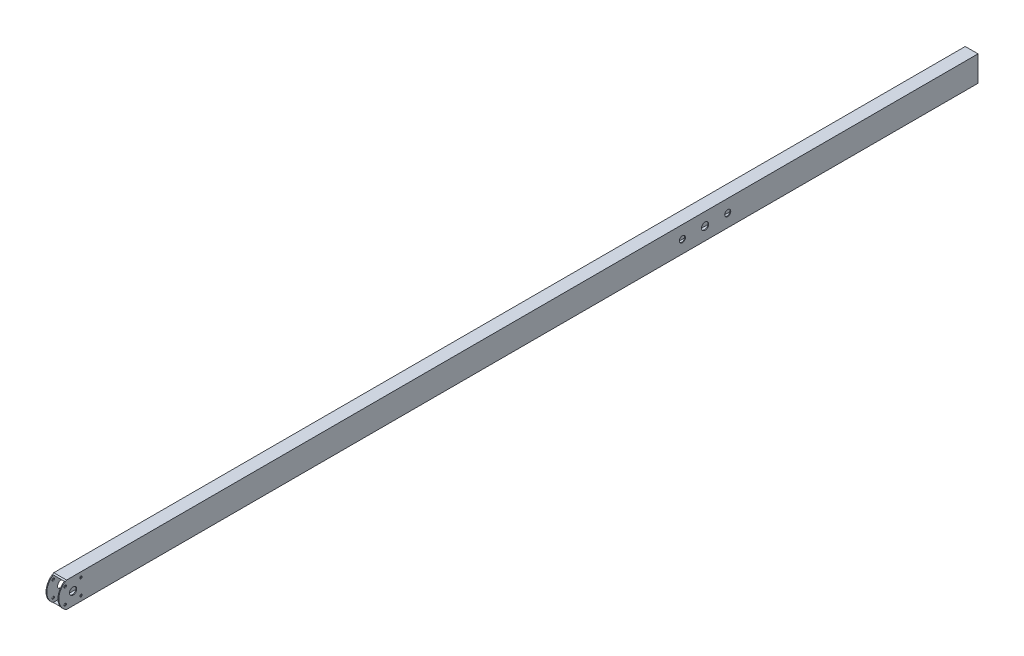
SolidWorks part; units mm, degrees
ref_plane "Front Plane" through (0, 0, 0) normal (0, 0, 1) x (1, 0, 0)
ref_plane "Top Plane" through (0, 0, 0) normal (0, 1, 0) x (1, 0, 0)
ref_plane "Right Plane" through (0, 0, 0) normal (1, 0, 0) x (0, 0, -1)
sketch "Sketch2" plane through (0, 0, 0) normal (0, 0, 1) x (1, 0, 0)
  line L1 (12.7, -25.4) -> (-12.7, -25.4)
  line L2 (12.7, -25.4) -> (12.7, 25.4)
  line L3 (12.7, 25.4) -> (-12.7, 25.4)
  line L4 (-12.7, -25.4) -> (-12.7, 25.4)
  line L5 (12.7, -25.4) -> (-12.7, 25.4) construction
  line L6 (12.7, 25.4) -> (-12.7, -25.4) construction
  point P1 (0, 0)
  dimension "D1" = 25.4
  dimension "D2" = 50.8
extrude "Extrude-Thin2" add sketch "Sketch2" along normal blind 1828.8 thin
sketch "Sketch8" plane through (12.7, 0, 0) normal (1, 0, 0) x (0, 0, -1)
  line L3 (-1800.225, -28.575) -> (-1800.225, 28.575)
  line L7 (0, -25.4) -> (0, 25.4)
  line L8 (0, 25.4) -> (-1828.8, 25.4)
  line L9 (-1828.8, 25.4) -> (-1828.8, -25.4)
  line L10 (-1828.8, -25.4) -> (0, -25.4)
  line L11 (0, -25.4) -> (0, 25.4)
  line L12 (0, 25.4) -> (-1828.8, 25.4)
  line L13 (-1828.8, 25.4) -> (-1828.8, -25.4)
  line L14 (-1828.8, -25.4) -> (0, -25.4)
  arc A0 (-1800.225, 28.575) -> (-1800.225, -28.575) centre (-1800.225, 0) ccw
  point P4 (-1828.8, 0)
  point P5 (-1828.8, 0)
  line M13 (-1828.8, 25.4) -> (-1828.8, -25.4)
  line M14 (-1828.8, -25.4) -> (0, -25.4)
  dimension "D2" = 57.15
  dimension "D1" = 0
extrude "Cut-Extrude1" cut sketch "Sketch8" against normal through all contours A0 L12 M13 | A0 L13 M14
hole_wizard "9/16 (0.5625) Diameter Hole1" positions "Sketch9" profile "Sketch10" hole size "9/16" standard "ANSI Inch" end condition through all
sketch "Sketch9" plane through (12.7, 0, 0) normal (1, 0, 0) x (0, 0, -1)
  arc A0 (-1813.3159, 25.4) -> (-1813.3159, -25.4) centre (-1800.225, 0) ccw construction
  point P0 (-1800.225, 0)
  point P3 (-1800.225, 0)
  point P4 (0, 0)
  point P5 (-1798.1492, 0)
  point P6 (0, 0)
  point P10 (-1828.8, 0)
  point P11 (0, 0)
  point P12 (-1800.225, 0)
sketch "Sketch10" plane through (12.7, 0, 1800.225) normal (0, 1, 0) x (0, 0, -1)
  line L0 (0, 0) -> (0, 25.4)
  line L1 (0, 25.4) -> (7.1437, 25.4)
  line L2 (7.1437, 25.4) -> (7.1437, 0)
  line L5 (7.1437, 0) -> (0, 0)
  line L11 (0, -6.35) -> (0, 107.95) construction
  dimension "Thru Hole Dia." = 14.2875
  dimension "Thru Hole Depth" = 25.4
sketch "Sketch3" plane through (12.7, 0, 0) normal (1, 0, 0) x (0, 0, -1)
  line L0 (-587.9703, 0) -> (-497.8797, 0)
  line L8 (-1813.3159, 25.4) -> (0, 25.4) construction
  line L9 (-1813.3159, -25.4) -> (0, -25.4) construction
  line L10 (-542.925, 25.4) -> (-542.925, -25.4) construction
  circle A0 centre (-1800.225, 0) radius 7.1438 construction
  point P0 (-542.925, 0)
  point P8 (-542.925, 0)
  point P18 (-542.925, 0)
  point P20 (-1796.2131, -1.0052)
  point P23 (-1763.649, 35.2561)
  dimension "D2" = 90.0906
  dimension "D1" = 1257.3
hole_wizard "9/16 (0.5625) Diameter Hole2" positions "Sketch4" profile "Sketch5" hole size "9/16" standard "ANSI Inch" end condition through all
sketch "Sketch4" plane through (12.7, 0, 0) normal (1, 0, 0) x (0, 0, -1)
  point P0 (-542.925, 0)
sketch "Sketch5" plane through (12.7, 0, 542.925) normal (0, 1, 0) x (0, 0, -1)
  line L0 (0, 0) -> (0, 25.4)
  line L1 (0, 25.4) -> (7.1437, 25.4)
  line L2 (7.1437, 25.4) -> (7.1437, 0)
  line L5 (7.1437, 0) -> (0, 0)
  line L11 (0, -6.35) -> (0, 107.95) construction
  dimension "Thru Hole Dia." = 14.2875
  dimension "Thru Hole Depth" = 25.4
hole_wizard "Ø12.0mm Dowel Hole1" positions "Sketch11" profile "Sketch12" hole size "Ø12.0" standard "ANSI Metric" end condition through all
sketch "Sketch11" plane through (12.7, 0, 0) normal (1, 0, 0) x (0, 0, -1)
  point P0 (-587.9703, 0)
  point P3 (-497.8797, 0)
sketch "Sketch12" plane through (12.7, 0, 587.9703) normal (0, 1, 0) x (0, 0, -1)
  line L0 (0, 0) -> (0, 25.4)
  line L1 (0, 25.4) -> (6, 25.4)
  line L2 (6, 25.4) -> (6, 0)
  line L5 (6, 0) -> (0, 0)
  line L11 (0, -6.35) -> (0, 107.95) construction
  dimension "Thru Hole Dia." = 12
  dimension "Thru Hole Depth" = 25.4
sketch "Sketch13" plane through (12.7, 0, 0) normal (1, 0, 0) x (0, 0, -1)
  circle A0 centre (-1800.225, 0) radius 27.813 construction
  circle A1 centre (-1800.225, 0) radius 27.813
  circle A2 centre (-1815.9404, -15.7154) radius 2.2479 construction
  circle A3 centre (-1815.9404, 15.7154) radius 2.2479 construction
  circle A4 centre (-1784.5096, -15.7154) radius 2.2479 construction
  circle A5 centre (-1784.5096, 15.7154) radius 2.2479 construction
  circle A6 centre (-1815.9404, -15.7154) radius 2.2479
  circle A7 centre (-1815.9404, 15.7154) radius 2.2479
  circle A8 centre (-1784.5096, -15.7154) radius 2.2479
  circle A9 centre (-1784.5096, 15.7154) radius 2.2479
hole_wizard "3/16 (0.1875) Diameter Hole1" positions "Sketch14" profile "Sketch15" hole size "3/16" standard "ANSI Inch" end condition through all
sketch "Sketch14" plane through (12.7, 0, 0) normal (1, 0, 0) x (0, 0, -1)
  point P0 (-1784.5096, 15.7154)
  point P2 (-1784.5096, -15.7154)
  point P5 (-1815.9404, -15.7154)
  point P8 (-1815.9404, 15.7154)
sketch "Sketch15" plane through (12.7, 15.7154, 1784.5096) normal (0, 1, 0) x (0, 0, -1)
  line L0 (0, 0) -> (0, 25.4)
  line L1 (0, 25.4) -> (2.3812, 25.4)
  line L2 (2.3812, 25.4) -> (2.3812, 0)
  line L5 (2.3812, 0) -> (0, 0)
  line L11 (0, -6.35) -> (0, 107.95) construction
  dimension "Thru Hole Dia." = 4.7625
  dimension "Thru Hole Depth" = 25.4
equation "\"H\"=2"
equation "\"W\"= 1"
equation "\"Wall\"= 1 / 16"
equation "\"D1@Sketch2\"=\"W\""
equation "\"D2@Sketch2\"= \"H\""
equation "\"D5@Extrude-Thin2\"=\"Wall\""
equation "\"FHspacing\"= 3 + 35 / 64"
equation "\"L\"=72"
equation "\"D1@Extrude-Thin2\"=\"L\""
equation "\"D2@Sketch3\"=\"FHspacing\""
equation "\"Shaft2Shaft\"= 49.5"
equation "\"D1@Sketch3\"=\"Shaft2Shaft\""
